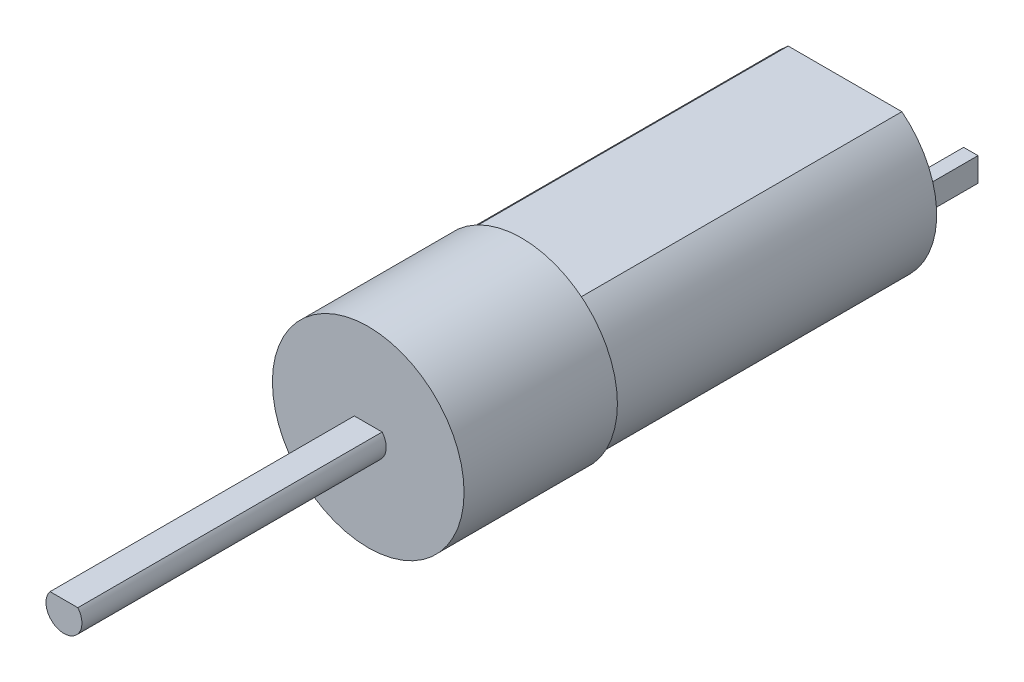
SolidWorks part; units mm, degrees
ref_plane "Front Plane" through (0, 0, 0) normal (0, 0, 1) x (1, 0, 0)
ref_plane "Top Plane" through (0, 0, 0) normal (0, 1, 0) x (1, 0, 0)
ref_plane "Right Plane" through (0, 0, 0) normal (1, 0, 0) x (0, 0, -1)
sketch "Sketch1" plane through (0, 0, 0) normal (0, 0, 1) x (1, 0, 0)
  circle A0 centre (0, 0) radius 8
  dimension "D1" = 16
extrude "Boss-Extrude1" add sketch "Sketch1" along normal blind 12.8 contours A0
sketch "Sketch2" plane through (0, 0, 12.8) normal (0, 0, 1) x (1, 0, 0)
  circle A0 centre (0, 0) radius 3
  dimension "D1" = 6
extrude "Boss-Extrude2" [suppressed] add sketch "Sketch2" along normal blind 3
sketch "Sketch3" plane through (0, 0, 0) normal (0, 0, -1) x (-1, 0, 0)
  circle A0 centre (0, 0) radius 7.65
  dimension "D1" = 15.3
extrude "Boss-Extrude3" add sketch "Sketch3" along normal blind 27
sketch "Sketch4" plane through (0, 0, -27) normal (0, 0, -1) x (-1, 0, 0)
  line L1 (-4.7458, -6) -> (4.7458, -6)
  line L3 (-4.7458, 6) -> (4.7458, 6)
  circle A0 centre (0, 0) radius 7.65 construction
  arc A1 (-4.7458, -6) -> (4.7458, -6) centre (0, 0) ccw
  arc A2 (4.7458, 6) -> (-4.7458, 6) centre (0, 0) ccw
  point P0 (0, 0)
  dimension "D1" = 12
extrude "Cut-Extrude1" cut sketch "Sketch4" against normal blind 27
sketch "Sketch7" plane through (0, 0, 12.8) normal (0, 0, 1) x (1, 0, 0)
  line L3 (-1.1608, 0.95) -> (1.1608, 0.95)
  arc A0 (-1.1608, 0.95) -> (1.1608, 0.95) centre (0, 0) ccw
  dimension "D1" = 3
  dimension "D2" = 0.95
extrude "Boss-Extrude4" add sketch "Sketch7" along normal blind 25.4
sketch "Sketch8" plane through (0, 0, -27) normal (0, 0, -1) x (-1, 0, 0)
  line L1 (-6.1, -1) -> (-4.9, -1)
  line L2 (-6.1, -1) -> (-6.1, 1)
  line L3 (-6.1, 1) -> (-4.9, 1)
  line L4 (-4.9, -1) -> (-4.9, 1)
  line L5 (-6.1, -1) -> (-4.9, 1) construction
  line L6 (-6.1, 1) -> (-4.9, -1) construction
  line L7 (0, 6.8343) -> (0, -6.6405) construction
  line L8 (6.1, -1) -> (4.9, 1) construction
  line L9 (6.1, 1) -> (4.9, -1) construction
  line L10 (6.1, -1) -> (4.9, -1)
  line L11 (4.9, -1) -> (4.9, 1)
  line L12 (6.1, -1) -> (6.1, 1)
  line L13 (6.1, 1) -> (4.9, 1)
  point P0 (-5.5, 0)
  dimension "D1" = 2
  dimension "D2" = 1.2
  dimension "D3" = 0
  dimension "D4" = 5.5
extrude "Boss-Extrude5" add sketch "Sketch8" along normal blind 5
